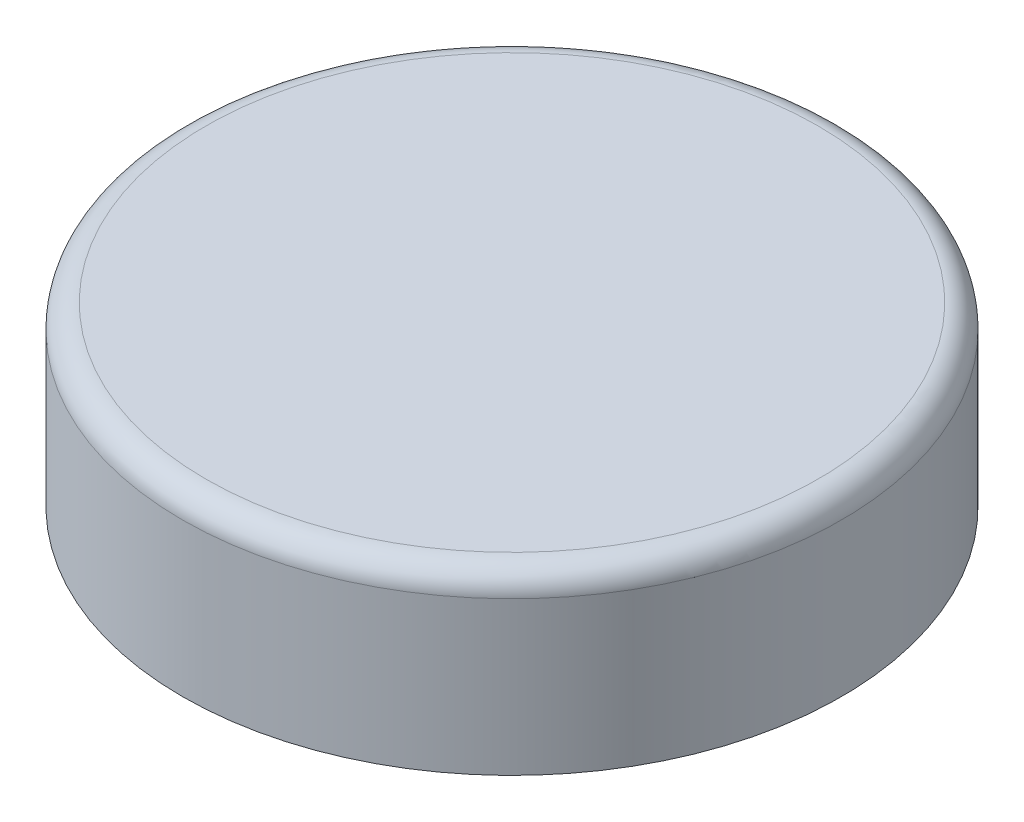
SolidWorks part; units mm, degrees
ref_plane "Front Plane" through (0, 0, 0) normal (0, 0, 1) x (1, 0, 0)
ref_plane "Top Plane" through (0, 0, 0) normal (0, 1, 0) x (1, 0, 0)
ref_plane "Right Plane" through (0, 0, 0) normal (1, 0, 0) x (0, 0, -1)
sketch "Sketch1" plane through (0, 0, 0) normal (0, 1, 0) x (1, 0, 0)
  circle A0 centre (0, 0) radius 25
  circle A1 centre (0, 0) radius 28
extrude "Boss-Extrude1" add sketch "Sketch1" along normal blind 15
sketch "Sketch2" plane through (0, 15, 0) normal (0, 1, 0) x (1, 0, 0)
  circle A0 centre (0, 0) radius 25.2898
extrude "Boss-Extrude2" add sketch "Sketch2" against normal blind 1.5
fillet "Fillet1" radius 2 1 edges at (0, 15, 28)
